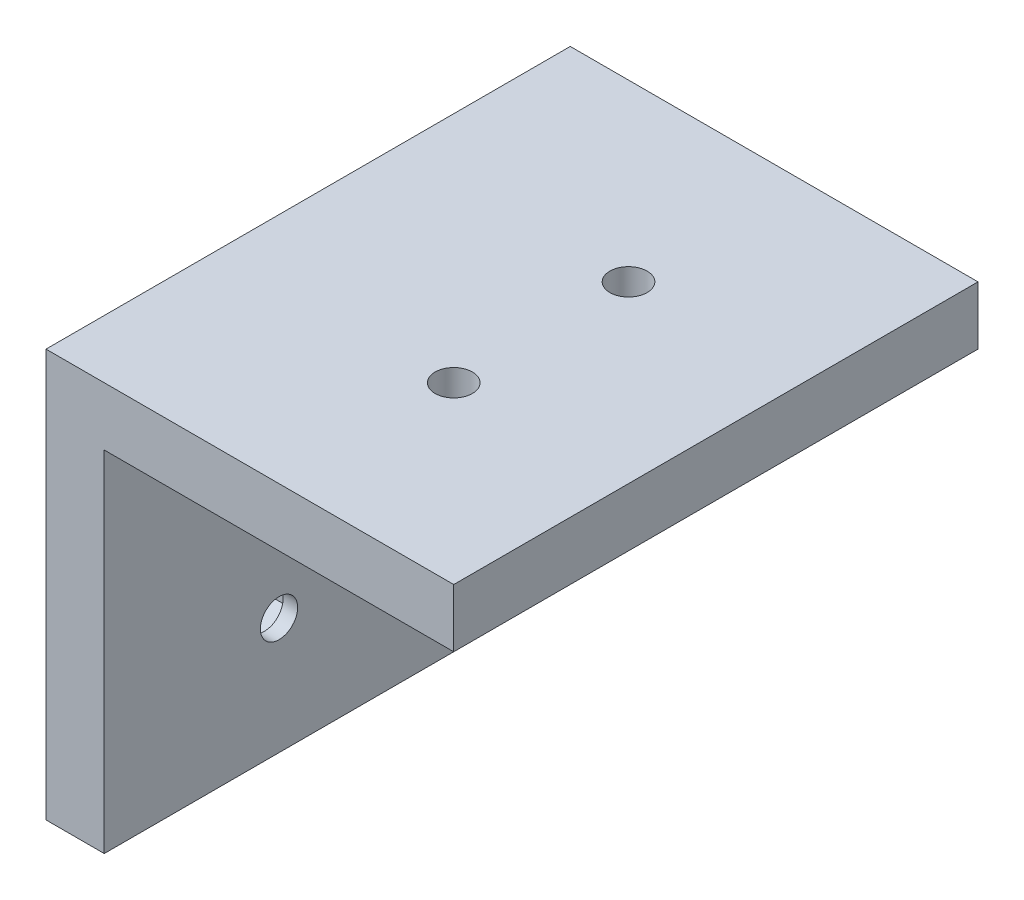
SolidWorks part; units mm, degrees
ref_plane "Front Plane" through (0, 0, 0) normal (0, 0, 1) x (1, 0, 0)
ref_plane "Top Plane" through (0, 0, 0) normal (0, 1, 0) x (1, 0, 0)
ref_plane "Right Plane" through (0, 0, 0) normal (1, 0, 0) x (0, 0, -1)
sketch "Sketch1" plane through (0, 0, 0) normal (0, 0, 1) x (1, 0, 0)
  line L0 (0, 0) -> (0, -30)
  line L1 (0, -30) -> (-5, -30)
  line L2 (0, 0) -> (30, 0)
  line L3 (30, 0) -> (30, 5)
  line L4 (-5, -30) -> (-5, 5)
  line L5 (-5, 5) -> (30, 5)
  dimension "D1" = 5
  dimension "D2" = 5
  dimension "D3" = 30
  dimension "D4" = 30
extrude "Boss-Extrude1" add sketch "Sketch1" along normal blind 45
sketch "Sketch2" plane through (0, 0, 0) normal (1, 0, 0) x (0, 0, -1)
  line L0 (-45, -30) -> (-45, -20) construction
  line L2 (-45, -30) -> (-45, 0) construction
  line L3 (-45, -20) -> (-30, -20) construction
  line L4 (-30, -20) -> (-15, -20) construction
  circle A0 centre (-30, -20) radius 1.6
  circle A1 centre (-15, -20) radius 1.6
  dimension "D4" = 3.2
  dimension "D5" = 3.2
  dimension "D1" = 15
  dimension "D2" = 15
  dimension "D3" = 10
extrude "Cut-Extrude1" cut sketch "Sketch2" against normal up to next
sketch "Sketch3" plane through (0, 0, 0) normal (0, -1, 0) x (1, 0, 0)
  line L0 (15, 45) -> (15, 30) construction
  line L1 (0, 45) -> (30, 45) construction
  line L2 (15, 30) -> (15, 15) construction
  circle A0 centre (15, 30) radius 1.6
  circle A1 centre (15, 15) radius 1.6
  dimension "D3" = 3.2
  dimension "D4" = 3.2
  dimension "D1" = 15
  dimension "D2" = 15
extrude "Cut-Extrude2" cut sketch "Sketch3" against normal up to next
sketch "Sketch4" plane through (0, 0, 0) normal (1, 0, 0) x (0, 0, -1)
  line L1 (-30, -23.4352) -> (-27.025, -21.7176)
  line L2 (-27.025, -21.7176) -> (-27.025, -18.2824)
  line L3 (-27.025, -18.2824) -> (-30, -16.5648)
  line L4 (-30, -16.5648) -> (-32.975, -18.2824)
  line L5 (-32.975, -18.2824) -> (-32.975, -21.7176)
  line L6 (-32.975, -21.7176) -> (-30, -23.4352)
  line L7 (-15, -23.4352) -> (-12.025, -21.7176)
  line L8 (-12.025, -21.7176) -> (-12.025, -18.2824)
  line L9 (-12.025, -18.2824) -> (-15, -16.5648)
  line L10 (-15, -16.5648) -> (-17.975, -18.2824)
  line L11 (-17.975, -18.2824) -> (-17.975, -21.7176)
  line L12 (-17.975, -21.7176) -> (-15, -23.4352)
  circle A0 centre (-30, -20) radius 2.975 construction
  circle A1 centre (-15, -20) radius 2.975 construction
  dimension "D1" = 5.95
  dimension "D2" = 5.95
extrude "Cut-Extrude3" cut sketch "Sketch4" against normal blind 2.5 from offset 1.25 offset against normal yes
